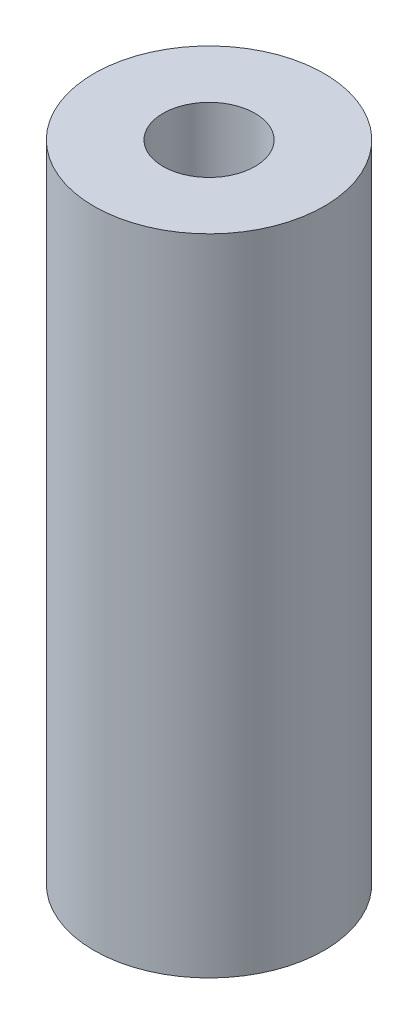
SolidWorks part; units mm, degrees
material "6061-T6 (SS)"
ref_plane "Front Plane" through (0, 0, 0) normal (0, 0, 1) x (1, 0, 0)
ref_plane "Top Plane" through (0, 0, 0) normal (0, 1, 0) x (1, 0, 0)
ref_plane "Right Plane" through (0, 0, 0) normal (1, 0, 0) x (0, 0, -1)
sketch "Sketch1" plane through (0, 0, 0) normal (0, 1, 0) x (1, 0, 0)
  circle A0 centre (0, 0) radius 2.5
  circle A1 centre (0, 0) radius 1
  dimension "D1" = 5
extrude "Boss-Extrude1" add sketch "Sketch1" along normal blind 14
